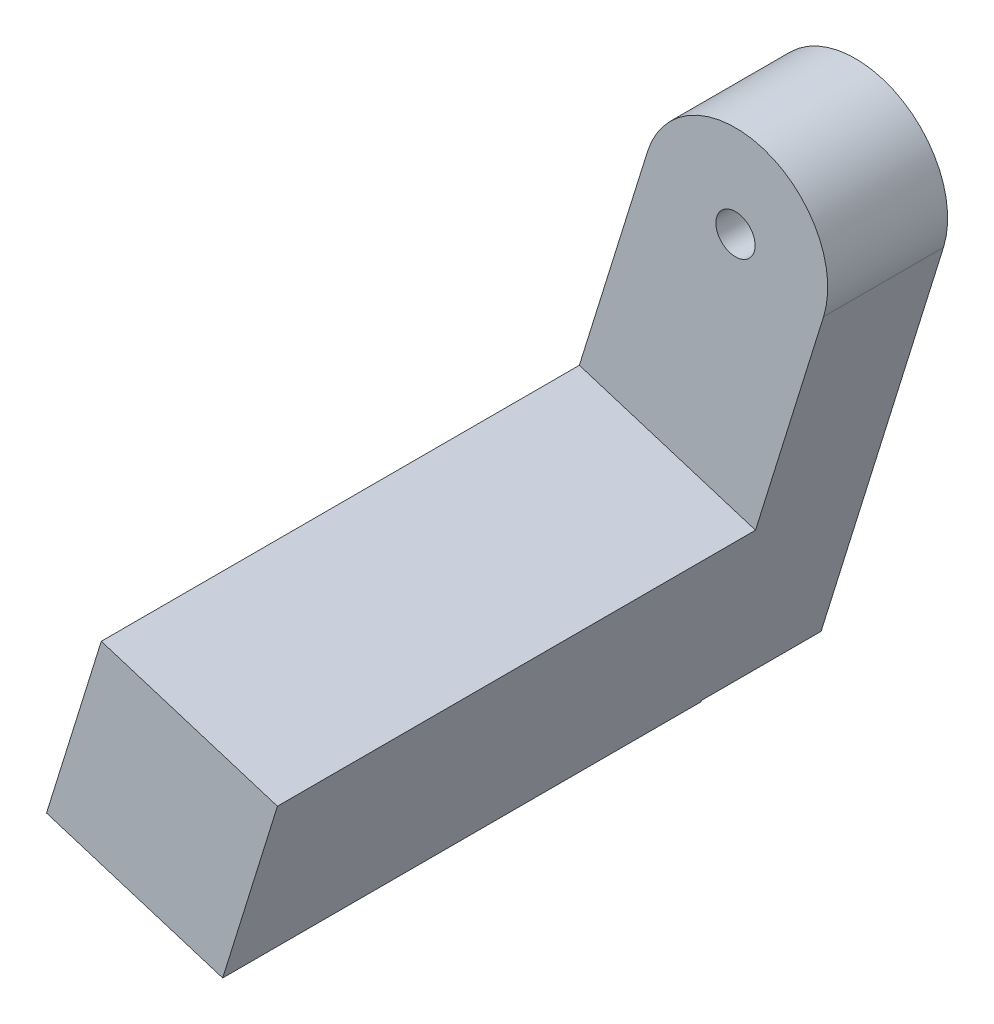
SolidWorks part; units mm, degrees
ref_plane "Front Plane" through (0, 0, 0) normal (0, 0, 1) x (1, 0, 0)
ref_plane "Top Plane" through (0, 0, 0) normal (0, 1, 0) x (1, 0, 0)
ref_plane "Right Plane" through (0, 0, 0) normal (1, 0, 0) x (0, 0, -1)
sketch "Sketch1" plane through (0, 0, 0) normal (0, 0, 1) x (1, 0, 0)
  circle A0 centre (0, 0) radius 2.3
  arc A1 (-2.3, 0) -> (2.3, 0) centre (0, 0) ccw construction
  circle A2 centre (0, 0) radius 4
  dimension "D1" = 8
extrude "Boss-Extrude1" add sketch "Sketch1" against normal up to surface (3.2 mm away)
sketch "Sketch2" plane through (0, 0, 0) normal (0, 0, 1) x (1, 0, 0)
  circle A0 centre (0, 0) radius 0.85
  circle A1 centre (0, 0) radius 4
extrude "Boss-Extrude2" add sketch "Sketch2" along normal blind 2
ref_plane "Plane1" through (3.8197, -1.1875, 0) normal (0.9549, -0.2969, 0) x (0, 0, -1)
sketch "Sketch5" plane through (3.8197, -1.1875, 0) normal (0.9549, -0.2969, 0) x (0, 0, -1)
  line L0 (-2, 0) -> (3.2, 0)
  line L1 (-2, 0) -> (-2, -9.9443)
  line L2 (3.2, 0) -> (3.2, -17.8789)
  line L3 (-2, -17.8789) -> (3.2, -17.8789)
  line L4 (-2, 4) -> (-2, -4) construction
  line L5 (3.2, -4) -> (3.2, 4) construction
  line L6 (-22.7319, -9.9443) -> (-2, -9.9443)
  line L7 (-22.7319, -9.9443) -> (-22.7319, -17.9443)
  line L8 (-2, -17.8789) -> (-2, -17.9443)
  line L9 (-22.7319, -17.9443) -> (-2, -17.9443)
  point P8 (-3, -4.8921)
  point P14 (-22.7319, -14.77)
  point P15 (-3, -14.77)
  point P17 (0, 0)
  point P18 (-3, -9.9443)
  dimension "D1" = 8
extrude "Boss-Extrude3" add sketch "Sketch5" against normal blind 8
sketch "Sketch6" plane through (0, 0, 2) normal (0, 0, 1) x (1, 0, 0)
  circle A0 centre (0, 0) radius 0.85
  dimension "D1" = 1.7
extrude "Cut-Extrude1" cut sketch "Sketch6" against normal blind 2
